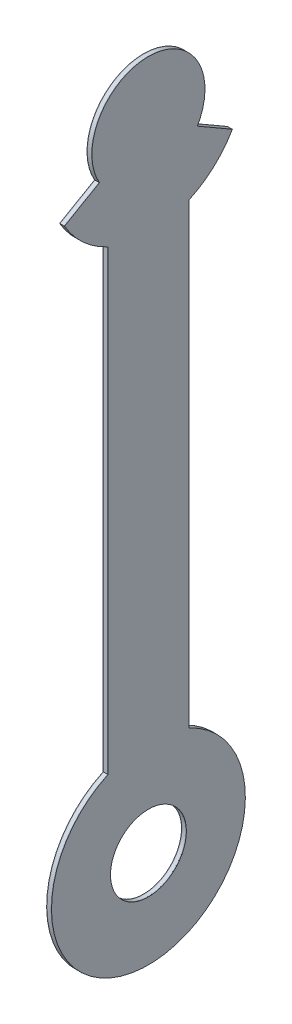
SolidWorks part; units mm, degrees
ref_plane "Front Plane" through (0, 0, 0) normal (0, 0, 1) x (1, 0, 0)
ref_plane "Top Plane" through (0, 0, 0) normal (0, 1, 0) x (1, 0, 0)
ref_plane "Right Plane" through (0, 0, 0) normal (1, 0, 0) x (0, 0, -1)
sketch "Sketch1" plane through (0, 0, 0) normal (1, 0, 0) x (0, 0, -1)
  line L0 (0, 0) -> (0, -392) construction
  line L1 (-30.3109, -17.5) -> (-51.9615, -30)
  line L2 (30.3109, -17.5) -> (51.9615, -30)
  line L3 (-20.3516, -196) -> (25.0726, -196) construction
  line L4 (-25, 0) -> (25, 0) construction
  line L5 (-25, -54.5436) -> (-25, -337.4564)
  line L6 (25, -54.5436) -> (25, -337.4564)
  arc A0 (-51.9615, -30) -> (51.9615, -30) centre (0, 0) ccw
  circle A1 centre (0, 0) radius 35
  circle A2 centre (0, -392) radius 60
  circle A3 centre (0, -392) radius 23.5
  point P15 (0, 0)
  dimension "D1" = 120
  dimension "D2" = 70
  dimension "D4" = 47
  dimension "D3" = 392
  dimension "D5" = 50
extrude "Boss-Extrude1" add sketch "Sketch1" against normal blind 0.25 contours A1 | A1 L1 A0 L2 | A2 L6 A0 L5 | A2 A3
sketch "Sketch2" plane through (-0.25, 0, 0) normal (-1, 0, 0) x (0, 0, 1)
  line L4 (-30.3109, -17.5) -> (-51.9615, -30)
  line L5 (-25, -54.5436) -> (-25, -337.4564)
  line L6 (25, -337.4564) -> (25, -54.5436)
  line L7 (51.9615, -30) -> (30.3109, -17.5)
  line L8 (-30.3109, -17.5) -> (-51.9615, -30)
  line L9 (-25, -54.5436) -> (-25, -337.4564)
  line L10 (25, -337.4564) -> (25, -54.5436)
  line L11 (51.9615, -30) -> (30.3109, -17.5)
  circle A0 centre (0, -392) radius 23.5 construction
  circle A1 centre (0, -392) radius 23.5
  arc A4 (30.3109, -17.5) -> (-30.3109, -17.5) centre (0, 0) ccw
  arc A5 (-51.9615, -30) -> (-25, -54.5436) centre (0, 0) ccw
  arc A6 (-25, -337.4564) -> (25, -337.4564) centre (0, -392) ccw
  arc A7 (25, -54.5436) -> (51.9615, -30) centre (0, 0) ccw
  arc A8 (30.3109, -17.5) -> (-30.3109, -17.5) centre (0, 0) ccw
  arc A9 (-51.9615, -30) -> (-25, -54.5436) centre (0, 0) ccw
  arc A10 (-25, -337.4564) -> (25, -337.4564) centre (0, -392) ccw
  arc A11 (25, -54.5436) -> (51.9615, -30) centre (0, 0) ccw
  dimension "D1" = 0
extrude "Boss-Extrude2" add sketch "Sketch2" along normal blind 2.5 separate body contours A8 L8 A9 L9 A10 L10 A11 L11
sketch "Sketch4" plane through (-2.75, 0, 0) normal (-1, 0, 0) x (0, 0, 1)
  line L4 (51.9615, -30) -> (30.3109, -17.5)
  line L5 (-30.3109, -17.5) -> (-51.9615, -30)
  line L6 (-25, -54.5436) -> (-25, -337.4564)
  line L7 (25, -337.4564) -> (25, -54.5436)
  line L8 (51.9615, -30) -> (30.3109, -17.5)
  line L9 (-30.3109, -17.5) -> (-51.9615, -30)
  line L10 (-25, -54.5436) -> (-25, -337.4564)
  line L11 (25, -337.4564) -> (25, -54.5436)
  circle A0 centre (0, -392) radius 23.5 construction
  circle A1 centre (0, -392) radius 23.5
  arc A4 (30.3109, -17.5) -> (-30.3109, -17.5) centre (0, 0) ccw
  arc A5 (-51.9615, -30) -> (-25, -54.5436) centre (0, 0) ccw
  arc A6 (-25, -337.4564) -> (25, -337.4564) centre (0, -392) ccw
  arc A7 (25, -54.5436) -> (51.9615, -30) centre (0, 0) ccw
  arc A8 (30.3109, -17.5) -> (-30.3109, -17.5) centre (0, 0) ccw
  arc A9 (-51.9615, -30) -> (-25, -54.5436) centre (0, 0) ccw
  arc A10 (-25, -337.4564) -> (25, -337.4564) centre (0, -392) ccw
  arc A11 (25, -54.5436) -> (51.9615, -30) centre (0, 0) ccw
  dimension "D1" = 0
extrude "Boss-Extrude3" add sketch "Sketch4" along normal blind 0.25 separate body
